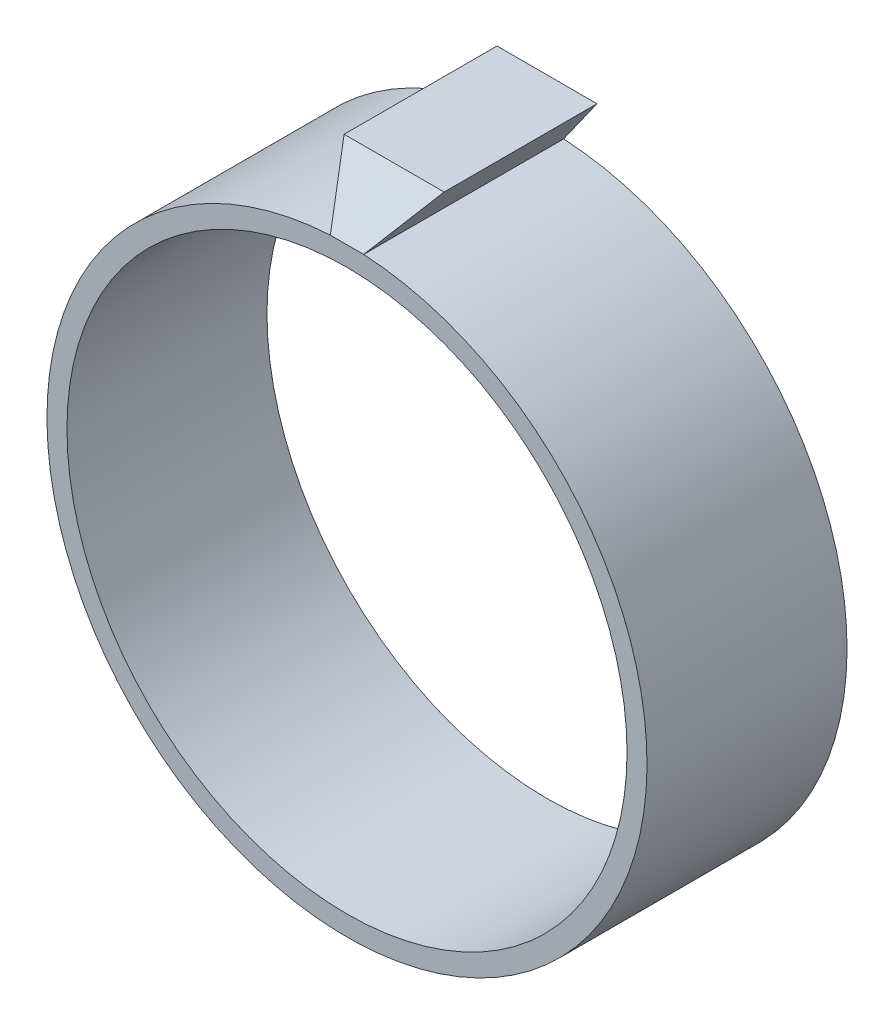
SolidWorks part; units mm, degrees
ref_plane "Front Plane" through (0, 0, 0) normal (0, 0, 1) x (1, 0, 0)
ref_plane "Top Plane" through (0, 0, 0) normal (0, 1, 0) x (1, 0, 0)
ref_plane "Right Plane" through (0, 0, 0) normal (1, 0, 0) x (0, 0, -1)
sketch "Sketch1" plane through (0, 0, 0) normal (0, 0, 1) x (1, 0, 0)
  line L0 (0, 42) -> (0, 52) construction
  line L3 (-7.5, 52) -> (7.5, 52)
  line L4 (-7.5, 52) -> (-2.5, 44.9305)
  line L5 (7.5, 52) -> (2.5, 44.9305)
  circle A0 centre (0, 0) radius 42
  arc A1 (-25, 33.7491) -> (25, 33.7491) centre (0, 0) cw
  arc A2 (26.7857, 36.1597) -> (-2.5, 44.9305) centre (0, 0) cw
  arc A3 (2.5, 44.9305) -> (26.7857, 36.1597) centre (0, 0) cw
  arc A4 (-26.7857, 36.1597) -> (26.7857, 36.1597) centre (0, 0) cw construction
  point P3 (-25, 33.7491)
  point P4 (25, 33.7491)
  point P16 (0, 52)
  point P18 (0, 47)
  dimension "D1" = 84
  dimension "D2" = 50
  dimension "D3" = 10
  dimension "D5" = 15
  dimension "D6" = 2.5
  dimension "D4" = 3
extrude "Boss-Extrude1" add sketch "Sketch1" along normal blind 30 contours A3 L5 L3 L4 A2 A0
sketch "Sketch3" plane through (0, 0, 0) normal (1, 0, 0) x (0, 0, -1)
  line L0 (-30, 44.9305) -> (-22.9305, 52)
  line L1 (-30, 52) -> (0, 52) construction
  line L5 (-22.9305, 52) -> (-30, 52)
  line L6 (-30, 52) -> (-30, 44.9305)
extrude "Cut-Extrude1" cut sketch "Sketch3" against normal up to surface and the other way up to surface up to face at (-5, 48.4653, 15) other way up to face at (5, 48.4653, 15)
